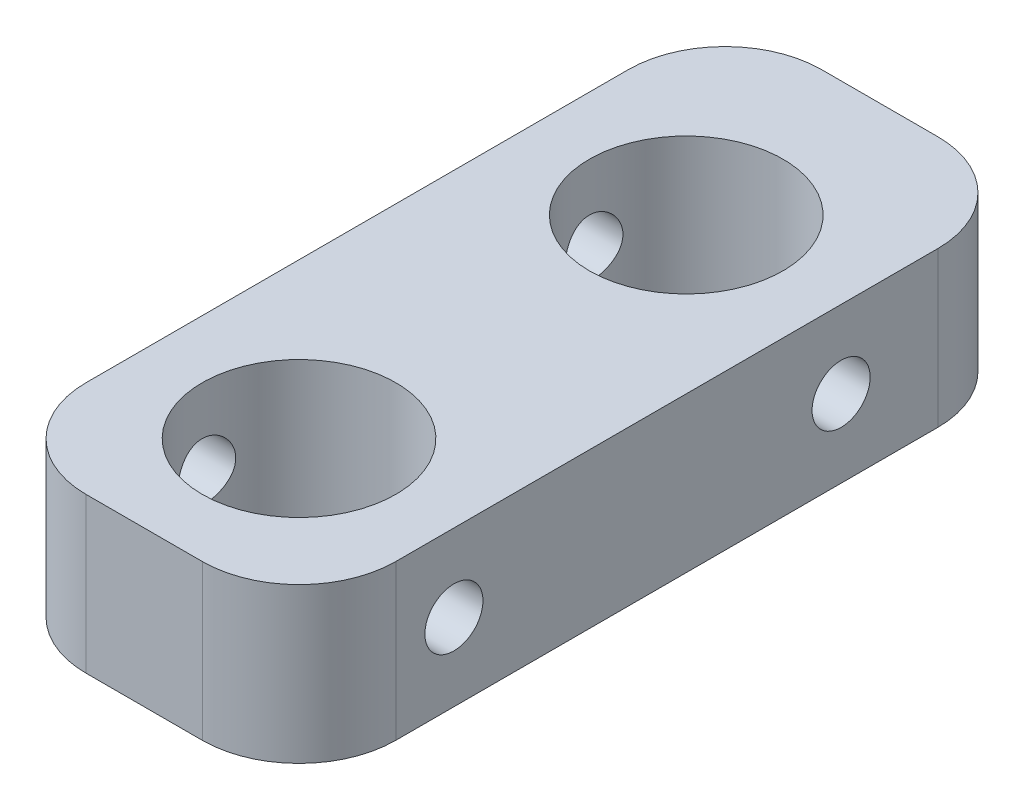
SolidWorks part; units mm, degrees
ref_plane "Front Plane" through (0, 0, 0) normal (0, 0, 1) x (1, 0, 0)
ref_plane "Top Plane" through (0, 0, 0) normal (0, 1, 0) x (1, 0, 0)
ref_plane "Right Plane" through (0, 0, 0) normal (1, 0, 0) x (0, 0, -1)
sketch "Sketch1" plane through (0, 0, 0) normal (0, 1, 0) x (1, 0, 0)
  line L1 (-2.6736, -35.3793) -> (3.3264, -35.3793)
  line L2 (-7.6736, -30.3793) -> (-7.6736, -2.3793)
  line L3 (-2.6736, 2.6207) -> (3.3264, 2.6207)
  line L4 (8.3264, -30.3793) -> (8.3264, -2.3793)
  arc A0 (3.3264, -35.3793) -> (8.3264, -30.3793) centre (3.3264, -30.3793) ccw
  arc A1 (3.3264, 2.6207) -> (8.3264, -2.3793) centre (3.3264, -2.3793) cw
  arc A2 (-2.6736, -35.3793) -> (-7.6736, -30.3793) centre (-2.6736, -30.3793) cw
  arc A3 (-7.6736, -2.3793) -> (-2.6736, 2.6207) centre (-2.6736, -2.3793) cw
  circle A4 centre (0.3264, -27.3793) radius 5
  circle A5 centre (0.3264, -7.3793) radius 5
  point P8 (8.3264, 2.6207)
  point P11 (-7.6736, -35.3793)
  point P14 (-7.6736, 2.6207)
  dimension "D3" = 5
  dimension "D4" = 10
  dimension "D1" = 16
  dimension "D2" = 38
  dimension "D5" = 8
extrude "Boss-Extrude1" add sketch "Sketch1" along normal blind 8
sketch "Sketch2" plane through (8.3264, 0, 0) normal (1, 0, 0) x (0, 0, -1)
  line L0 (2.6207, 8) -> (2.6207, 0) construction
  line L1 (-35.3793, 8) -> (-35.3793, 0) construction
  circle A0 centre (-27.3793, 4) radius 1.5
  circle A1 centre (-7.3793, 4) radius 1.5
  dimension "D1" = 10
  dimension "D2" = 8
extrude "Cut-Extrude1" cut sketch "Sketch2" against normal through all
